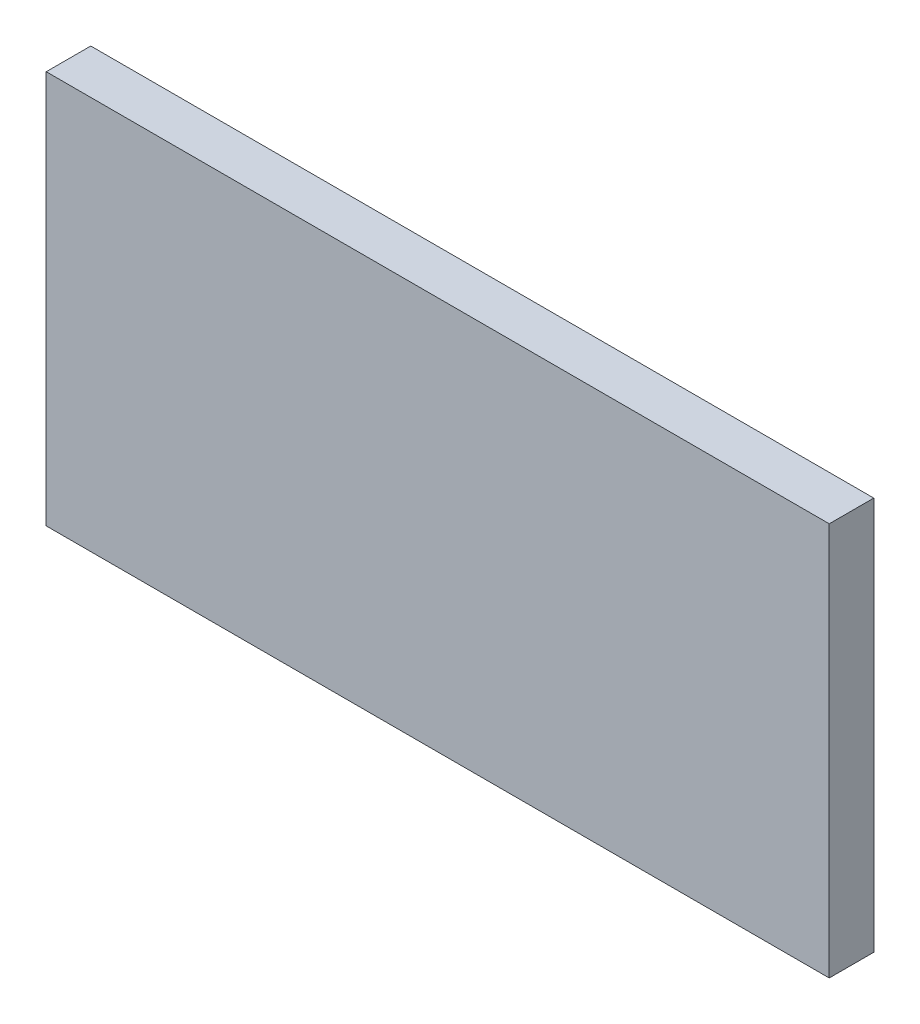
SolidWorks part; units mm, degrees
material "ABS PC"
ref_plane "Front Plane" through (0, 0, 0) normal (0, 0, 1) x (1, 0, 0)
ref_plane "Top Plane" through (0, 0, 0) normal (0, 1, 0) x (1, 0, 0)
ref_plane "Right Plane" through (0, 0, 0) normal (1, 0, 0) x (0, 0, -1)
sketch "Sketch1" plane through (0, 0, 0) normal (0, 0, 1) x (1, 0, 0)
  line L0 (-8.214, -113.0521) -> (-8.722, -113.5601) construction
  line L2 (4.6765, -106.8291) -> (5.1845, -106.3211) construction
  line L3 (-8.468, -113.3061) -> (4.9305, -113.3061)
  line L4 (-8.468, -113.3061) -> (-8.468, -106.5751)
  line L5 (-8.468, -106.5751) -> (4.9305, -106.5751)
  line L6 (4.9305, -113.3061) -> (4.9305, -106.5751)
  line L7 (-8.468, -113.3061) -> (4.9305, -106.5751) construction
  line L8 (-8.468, -106.5751) -> (4.9305, -113.3061) construction
  point P12 (-1.7687, -109.9406)
extrude "Boss-Extrude1" add sketch "Sketch1" along normal blind 0.762
